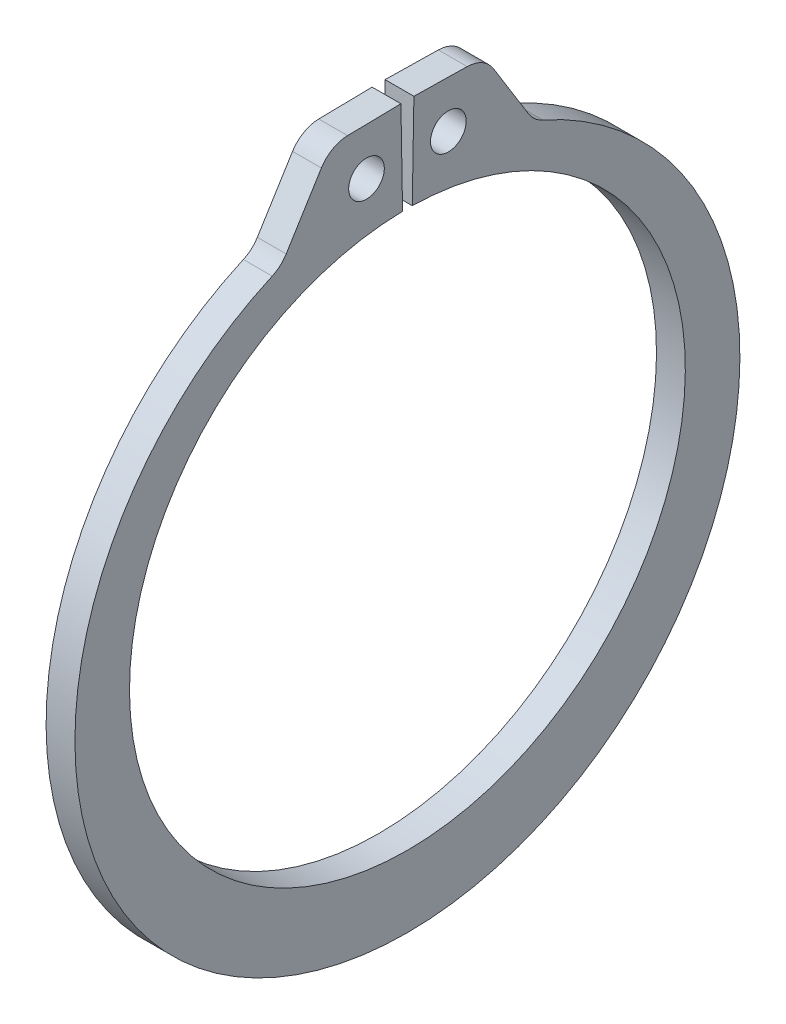
SolidWorks part; units mm, degrees
material "Cast Carbon Steel"
ref_plane "Front" through (0, 0, 0) normal (0, 0, 1) x (1, 0, 0)
ref_plane "Top" through (0, 0, 0) normal (0, 1, 0) x (1, 0, 0)
ref_plane "Right" through (0, 0, 0) normal (1, 0, 0) x (0, 0, -1)
sketch "Sketch1" plane through (0, 0, 0) normal (1, 0, 0) x (0, 0, -1)
  line L0 (0, 0) -> (0, 10.287) construction
  line L1 (-0.1795, 10.2854) -> (-0.2403, 13.7647)
  line L2 (0.2403, 13.7647) -> (2.8497, 13.7192)
  line L3 (2.8497, 13.7192) -> (4.6815, 10.7605)
  line L4 (0.1795, 10.2854) -> (0.2403, 13.7647)
  line L5 (-0.2403, 13.7647) -> (-2.8497, 13.7192)
  line L6 (-2.8497, 13.7192) -> (-4.6815, 10.7605)
  line L7 (-4.6815, 10.7605) -> (-4.1039, 9.4329) construction
  line L8 (4.6815, 10.7605) -> (4.1039, 9.4329) construction
  line L9 (0, -10.287) -> (0, -12.9286) construction
  line L10 (-2.8497, 13.7192) -> (-0.1795, 10.2854) construction
  line L11 (0, 10.287) -> (0, 13.7668) construction
  line L12 (-10.287, 0) -> (10.287, 0) construction
  circle A0 centre (0, 0) radius 10.287 construction
  arc A1 (-0.1795, 10.2854) -> (0.1795, 10.2854) centre (0, 0) ccw
  circle A3 centre (0, 0) radius 15.0495 construction
  circle A4 centre (-1.5146, 12.0023) radius 0.6604
  circle A5 centre (1.5146, 12.0023) radius 0.6604
  arc A6 (-4.6815, 10.7605) -> (4.6815, 10.7605) centre (0, -0.6214) ccw
  point P0 (0, -12.9286)
  dimension "A" = 20.574
  dimension "D2" = 2.6098
  dimension "L" = 30.099
  dimension "Hole" = 1.3208
  dimension "Smin" = 1.4478
  dimension "Smax" = 2.6416
  dimension "H" = 3.4798
  dimension "Angle" = 1
extrude "Extrude1" add sketch "Sketch1" along normal mid plane 1.0668
fillet "Fillet1" radius 1.1684 4 edges at (0, 10.7605, 4.6815) (0, 10.7605, -4.6815) (0, 13.7192, 2.8497) (0, 13.7192, -2.8497)
sketch "Sketch2" plane through (0, 0, 0) normal (0, 0, 1) x (1, 0, 0)
  line L0 (-5.9182, 0) -> (15.4178, 0)
  line L1 (15.4178, 0) -> (15.4178, -11.1125)
  line L2 (-0.5842, -11.1125) -> (-5.2324, -11.1125)
  line L3 (15.4178, -11.1125) -> (0.5842, -11.1125)
  line L4 (0.5842, -11.1125) -> (0.5842, -10.4267)
  line L5 (0.5842, -10.4267) -> (-0.5842, -10.4267)
  line L6 (-0.5842, -10.4267) -> (-0.5842, -11.1125)
  line L7 (-0.5842, -11.1125) -> (-5.9182, -11.1125) construction
  line L8 (-5.9182, -11.1125) -> (-5.9182, 0) construction
  line L9 (15.4178, 0) -> (76.391, 0) construction
  line L10 (-5.2324, -11.1125) -> (-5.9182, -10.4267)
  line L11 (-5.9182, -10.4267) -> (-5.9182, 0)
  point P10 (0, -10.4267)
  dimension "D1" = 45
  dimension "Dg" = 20.8534
  dimension "Ds" = 22.225
  dimension "W" = 1.1684
  dimension "D2" = 21.336
  dimension "D3" = 5.334
revolve "Revolve1" [suppressed] add sketch "Sketch2" angle 360 about L9
delete or keep bodies "Body-Delete1" [suppressed] type delete bodies bodies 122
equation "\"D2@Sketch2\" = \"D1@Extrude1\"*20"
equation "\"D3@Sketch2\" = \"D2@Sketch2\"/4"
equation "\"D2@Sketch1\" = \"H@Sketch1\"*.75"
